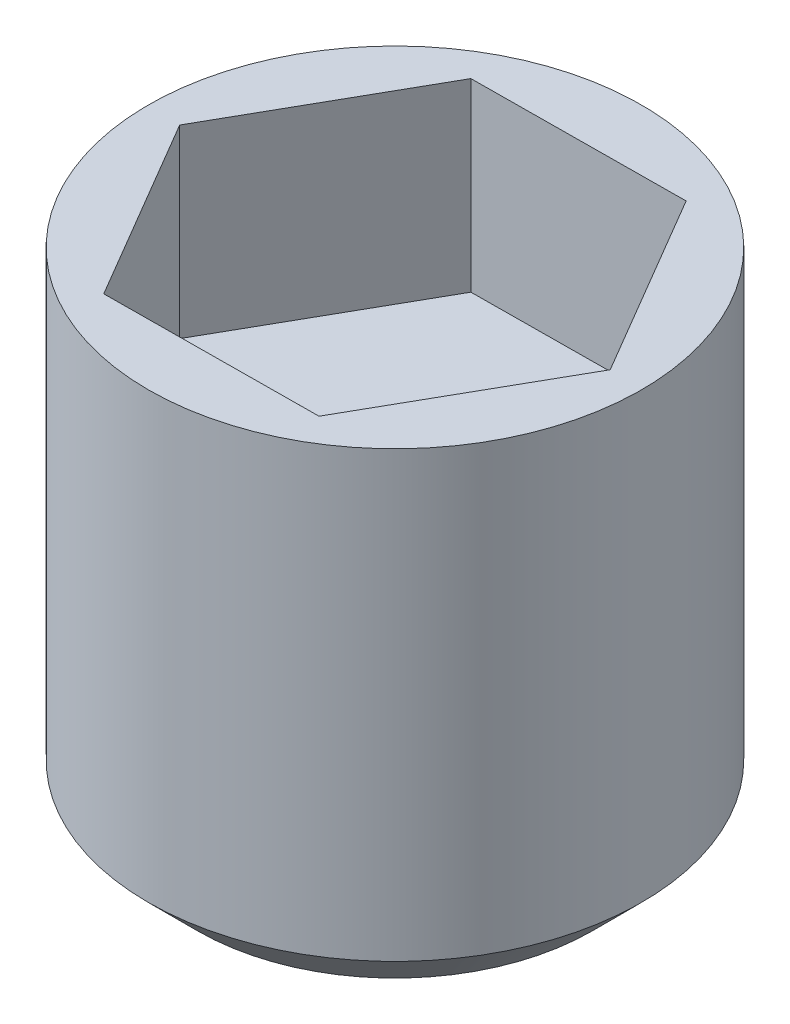
SolidWorks part; units mm, degrees
ref_plane "Спереди" through (0, 0, 0) normal (0, 0, 1) x (1, 0, 0)
ref_plane "Сверху" through (0, 0, 0) normal (0, 1, 0) x (1, 0, 0)
ref_plane "Справа" through (0, 0, 0) normal (1, 0, 0) x (0, 0, -1)
sketch "Эскиз1" plane through (0, 0, 0) normal (0, 0, 1) x (1, 0, 0)
  line L0 (0, 0) -> (3.2, 0)
  line L2 (4, 8) -> (4, 0.8)
  line L3 (4, 0.8) -> (3.2, 0)
  line L4 (4, 8) -> (0, 8)
  line L5 (0, 68.6446) -> (0, -29.1082) construction
  line L6 (0, 0) -> (0, 8)
  point P1 (0, 0)
revolve "Повернуть1" add sketch "Эскиз1" angle 360 about L5
sketch "Эскиз2" plane through (0, 8, 0) normal (0, 1, 0) x (1, 0, 0)
  line L1 (1.7553, -2.9865) -> (3.464, 0.0269)
  line L2 (3.464, 0.0269) -> (1.7087, 3.0133)
  line L3 (1.7087, 3.0133) -> (-1.7553, 2.9865)
  line L4 (-1.7553, 2.9865) -> (-3.464, -0.0269)
  line L5 (-3.464, -0.0269) -> (-1.7087, -3.0133)
  line L6 (-1.7087, -3.0133) -> (1.7553, -2.9865)
  circle A0 centre (0, 0) radius 3 construction
extrude "Вырез-Вытянуть1" cut sketch "Эскиз2" against normal blind 3
